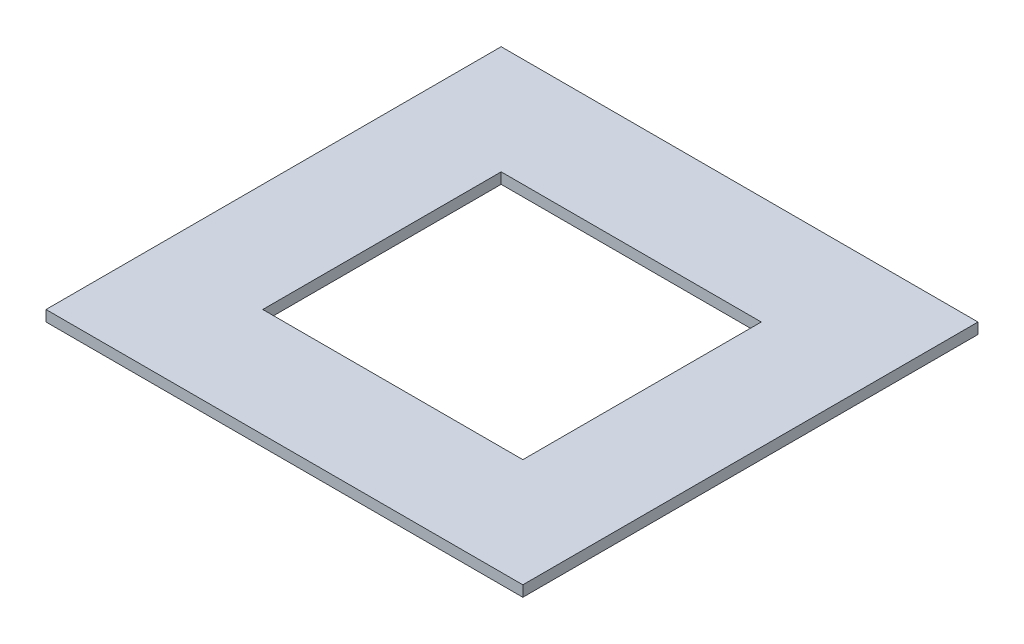
SolidWorks part; units mm, degrees
ref_plane "Front Plane" through (0, 0, 0) normal (0, 0, 1) x (1, 0, 0)
ref_plane "Top Plane" through (0, 0, 0) normal (0, 1, 0) x (1, 0, 0)
ref_plane "Right Plane" through (0, 0, 0) normal (1, 0, 0) x (0, 0, -1)
sketch "Sketch1" plane through (0, 0, 0) normal (0, 1, 0) x (1, 0, 0)
  line L1 (0, 0) -> (-139.7, 0)
  line L2 (0, 0) -> (0, 133.35)
  line L3 (0, 133.35) -> (-139.7, 133.35)
  line L4 (-139.7, 0) -> (-139.7, 133.35)
  line L5 (-107.95, 101.6) -> (-31.75, 101.6)
  line L6 (-107.95, 101.6) -> (-107.95, 31.75)
  line L7 (-107.95, 31.75) -> (-31.75, 31.75)
  line L8 (-31.75, 101.6) -> (-31.75, 31.75)
  dimension "D1" = 139.7
  dimension "D2" = 133.35
  dimension "D3" = 31.75
  dimension "D4" = 31.75
  dimension "D5" = 31.75
  dimension "D6" = 31.75
extrude "Boss-Extrude1" add sketch "Sketch1" along normal blind 3.175
